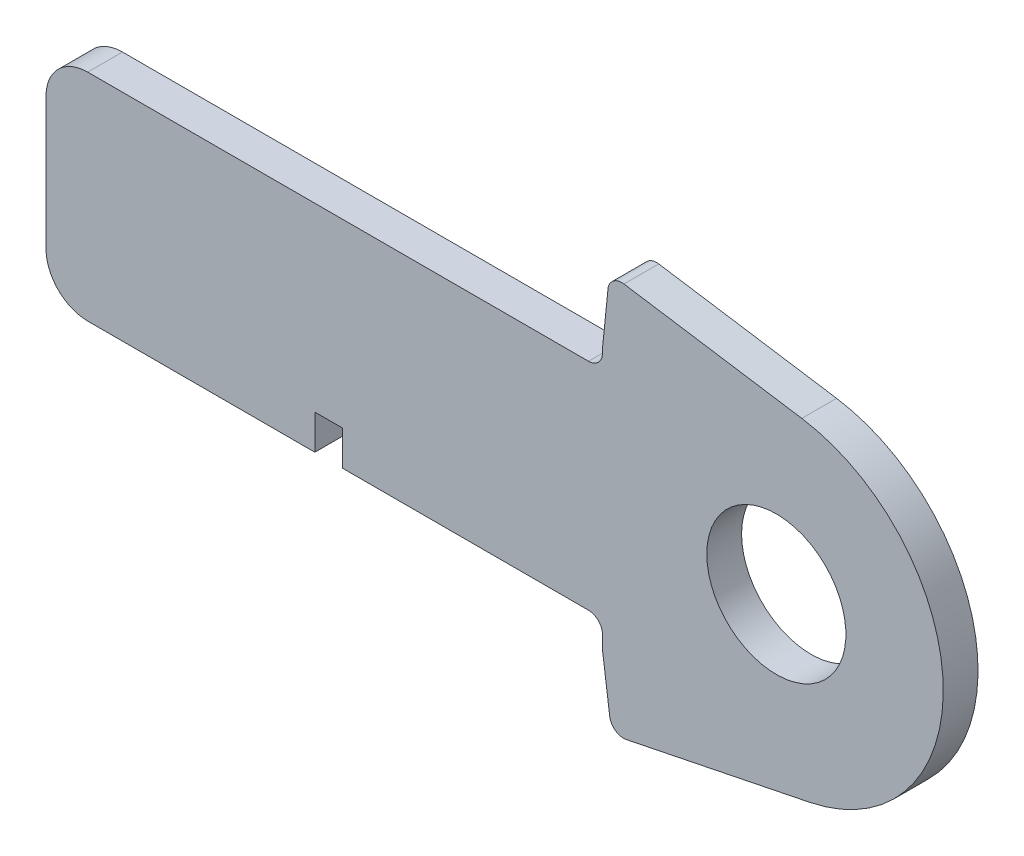
SolidWorks part; units mm, degrees
material "Plywood"
ref_plane "Front Plane" through (0, 0, 0) normal (0, 0, 1) x (1, 0, 0)
ref_plane "Top Plane" through (0, 0, 0) normal (0, 1, 0) x (1, 0, 0)
ref_plane "Right Plane" through (0, 0, 0) normal (1, 0, 0) x (0, 0, -1)
curve "Curve1"
  spline degree 3 poles (452.1031, 0.7048, 0) (452.0685, 0.7262, 0) (451.9301, 0.8117, 0) (451.6183, 1.003, 0) (451.099, 1.3216, 0) (450.372, 1.7653, 0) (449.438, 2.3329, 0) (448.2963, 3.0204, 0) (446.9478, 3.8257, 0) (445.3928, 4.7448, 0) (443.6314, 5.7736, 0) (441.6643, 6.9077, 0) (439.4916, 8.1409, 0) (437.1143, 9.468, 0) (434.5331, 10.8828, 0) (431.7485, 12.3789, 0) (428.7615, 13.9486, 0) (425.5733, 15.5853, 0) (422.1844, 17.2798, 0) (418.5964, 19.0251, 0) (414.8106, 20.8125, 0) (410.8282, 22.6325, 0) (406.6515, 24.4776, 0) (402.2816, 26.3365, 0) (397.7212, 28.201, 0) (392.972, 30.0605, 0) (388.0369, 31.9065, 0) (382.9178, 33.7272, 0) (377.6186, 35.5144, 0) (372.1418, 37.2567, 0) (366.4913, 38.9446, 0) (360.6704, 40.5671, 0) (354.684, 42.1159, 0) (348.5359, 43.5797, 0) (342.2312, 44.9487, 0) (335.775, 46.2147, 0) (329.1727, 47.3651, 0) (322.4425, 48.3989, 0) (315.6929, 49.2588, 0) (308.9571, 50.1023, 0) (302.2314, 50.8946, 0) (295.4235, 51.6533, 0) (288.5399, 52.3742, 0) (281.5875, 53.055, 0) (274.5733, 53.6928, 0) (267.5046, 54.2857, 0) (260.3883, 54.8303, 0) (253.2318, 55.3259, 0) (246.0422, 55.768, 0) (238.8272, 56.1563, 0) (231.5941, 56.4881, 0) (224.3504, 56.7611, 0) (217.1039, 56.9737, 0) (209.862, 57.1238, 0) (202.6326, 57.2105, 0) (195.4232, 57.2315, 0) (188.2416, 57.1863, 0) (181.0954, 57.0734, 0) (173.9924, 56.8912, 0) (166.9401, 56.6395, 0) (159.9462, 56.3182, 0) (153.0184, 55.9248, 0) (146.164, 55.4618, 0) (139.3909, 54.9271, 0) (132.7063, 54.3206, 0) (126.1174, 53.645, 0) (119.6314, 52.8983, 0) (113.2554, 52.0826, 0) (106.9962, 51.1996, 0) (100.8609, 50.2488, 0) (94.8561, 49.2329, 0) (88.9882, 48.153, 0) (83.2635, 47.0122, 0) (77.6882, 45.8109, 0) (72.2682, 44.5525, 0) (67.0092, 43.2395, 0) (61.9167, 41.874, 0) (56.9959, 40.4594, 0) (52.2519, 38.999, 0) (47.6902, 37.4943, 0) (43.3141, 35.951, 0) (39.1291, 34.3702, 0) (35.1384, 32.7568, 0) (31.3466, 31.113, 0) (27.7567, 29.4439, 0) (24.3726, 27.7512, 0) (21.1967, 26.0397, 0) (18.2324, 24.3122, 0) (15.4823, 22.5717, 0) (12.9477, 20.8227, 0) (10.632, 19.0664, 0) (8.5361, 17.307, 0) (6.6613, 15.5474, 0) (5.0102, 13.7886, 0) (3.5829, 12.0339, 0) (2.3811, 10.2847, 0) (1.4051, 8.5424, 0) (0.6571, 6.8085, 0) (0.1363, 5.084, 0) (-0.1488, 3.3712, 0) (-0.2197, 1.669, 0) (-0.0731, 0.5555, 0) (0, 0, 0) knots 0 0 0 0 0.000254 0.001015 0.002283 0.004057 0.006331 0.009105 0.012374 0.016134 0.02038 0.025106 0.030306 0.035972 0.0421 0.048678 0.055702 0.06316 0.071046 0.07935 0.088063 0.097176 0.106678 0.116562 0.126814 0.137428 0.148394 0.1597 0.171338 0.183298 0.19557 0.208144 0.221012 0.234162 0.247587 0.261277 0.275223 0.289414 0.303771 0.317689 0.331784 0.34604 0.360444 0.374983 0.38964 0.404403 0.419257 0.434187 0.449177 0.464215 0.479284 0.49437 0.509458 0.524532 0.539579 0.554583 0.56953 0.584403 0.599191 0.613877 0.628447 0.642889 0.657186 0.671326 0.685294 0.699078 0.712665 0.726043 0.739198 0.752118 0.764792 0.777208 0.789356 0.801224 0.812804 0.824083 0.835055 0.84571 0.856038 0.866034 0.875689 0.884998 0.893953 0.902553 0.910789 0.918661 0.926166 0.933303 0.940071 0.946475 0.952518 0.958205 0.963547 0.968557 0.97325 0.977651 0.981787 0.985694 0.989415 0.993001 0.996508 1 1 1 1
curve "Curve2"
  spline degree 3 poles (0, 0, 0) (0.1161, -0.5481, 0) (0.3488, -1.6467, 0) (0.9811, -3.2283, 0) (1.8173, -4.7487, 0) (2.8749, -6.2038, 0) (4.147, -7.5932, 0) (5.6306, -8.9184, 0) (7.3243, -10.1787, 0) (9.226, -11.3735, 0) (11.3328, -12.5041, 0) (13.6425, -13.5697, 0) (16.1528, -14.5701, 0) (18.8611, -15.5039, 0) (21.764, -16.3724, 0) (24.8588, -17.1737, 0) (28.1419, -17.9088, 0) (31.6103, -18.5759, 0) (35.26, -19.1755, 0) (39.0874, -19.7075, 0) (43.0885, -20.172, 0) (47.2594, -20.5682, 0) (51.596, -20.8969, 0) (56.0938, -21.1583, 0) (60.7487, -21.3533, 0) (65.556, -21.481, 0) (70.5112, -21.5436, 0) (75.6096, -21.5419, 0) (80.8464, -21.4754, 0) (86.2171, -21.3479, 0) (91.7164, -21.1586, 0) (97.3395, -20.9096, 0) (103.0813, -20.6036, 0) (108.9365, -20.2416, 0) (114.9002, -19.8251, 0) (120.967, -19.3576, 0) (127.1315, -18.8401, 0) (133.3883, -18.2757, 0) (139.7319, -17.6673, 0) (146.1567, -17.0167, 0) (152.6572, -16.327, 0) (159.2275, -15.6004, 0) (165.862, -14.8409, 0) (172.5546, -14.0497, 0) (179.2998, -13.2315, 0) (186.0911, -12.3877, 0) (192.923, -11.5217, 0) (199.7891, -10.6375, 0) (206.6832, -9.7349, 0) (213.5994, -8.8205, 0) (220.5311, -7.8935, 0) (227.4721, -6.9586, 0) (234.4161, -6.0188, 0) (241.3564, -5.0743, 0) (248.2868, -4.1291, 0) (255.2009, -3.1857, 0) (262.0918, -2.2442, 0) (268.9535, -1.3094, 0) (275.779, -0.3811, 0) (282.5619, 0.5389, 0) (289.2958, 1.4477, 0) (295.9744, 2.3443, 0) (302.5907, 3.228, 0) (309.138, 4.0992, 0) (315.5119, 4.9314, 0) (321.6955, 5.769, 0) (327.7099, 6.4556, 0) (333.6493, 7.0417, 0) (339.52, 7.5222, 0) (345.315, 7.9041, 0) (351.0275, 8.19, 0) (356.6509, 8.3839, 0) (362.1779, 8.4917, 0) (367.6017, 8.516, 0) (372.9148, 8.4647, 0) (378.1105, 8.3417, 0) (383.1813, 8.1528, 0) (388.1203, 7.9042, 0) (392.9205, 7.6027, 0) (397.5745, 7.2527, 0) (402.076, 6.8625, 0) (406.4179, 6.4377, 0) (410.5937, 5.9833, 0) (414.5972, 5.5086, 0) (418.4221, 5.0169, 0) (422.0625, 4.5163, 0) (425.5126, 4.0117, 0) (428.7669, 3.5097, 0) (431.8204, 3.015, 0) (434.6681, 2.5342, 0) (437.3055, 2.0718, 0) (439.7281, 1.6323, 0) (441.9324, 1.2212, 0) (443.9143, 0.8406, 0) (445.6709, 0.4968, 0) (447.199, 0.1913, 0) (448.4964, -0.0716, 0) (449.5609, -0.2909, 0) (450.3908, -0.463, 0) (450.9844, -0.5881, 0) (451.3411, -0.6626, 0) (451.4997, -0.6964, 0) (451.5393, -0.7048, 0) knots 0 0 0 0 0.003638 0.007293 0.011028 0.014901 0.018963 0.023258 0.027821 0.032679 0.037853 0.043362 0.049215 0.055422 0.061989 0.068918 0.076211 0.083868 0.091887 0.100266 0.109 0.118085 0.127515 0.137285 0.147388 0.157816 0.168563 0.179619 0.190977 0.202627 0.21456 0.226767 0.239236 0.251959 0.264924 0.27812 0.291536 0.30516 0.318981 0.332985 0.347163 0.361499 0.375981 0.390597 0.405333 0.420175 0.43511 0.450124 0.465203 0.480333 0.495501 0.51069 0.525887 0.541078 0.556247 0.571382 0.586466 0.601485 0.616424 0.631269 0.646007 0.660621 0.675098 0.689423 0.703582 0.716908 0.730009 0.742952 0.755726 0.76832 0.780724 0.792927 0.804916 0.816679 0.828204 0.839475 0.850481 0.861208 0.871639 0.881763 0.891564 0.901027 0.910139 0.918884 0.927249 0.935221 0.942785 0.949928 0.956638 0.962904 0.968712 0.974054 0.978918 0.983297 0.98718 0.990561 0.993433 0.995791 0.99763 0.998946 0.999737 1 1 1 1
sketch "Sketch1" plane through (0, 0, 0) normal (0, 0, 1) x (1, 0, 0)
  line L24 (435.3301, 0.6787) -> (439.1729, -1.6142)
  line L25 (434.7872, -0.6787) -> (439.1729, -1.6142)
  spline S4 degree 3 poles (0, 0) (0.1118, -0.5277) (0.3359, -1.5856) (0.9447, -3.1085) (1.7499, -4.5725) (2.7683, -5.9736) (3.9931, -7.3115) (5.4217, -8.5876) (7.0526, -9.8011) (8.8837, -10.9516) (10.9124, -12.0402) (13.1363, -13.0663) (15.5535, -14.0296) (18.1613, -14.9287) (20.9565, -15.765) (23.9365, -16.5366) (27.0978, -17.2444) (30.4375, -17.8867) (33.9519, -18.4641) (37.6373, -18.9763) (41.49, -19.4236) (45.5061, -19.8051) (49.6818, -20.1216) (54.0128, -20.3734) (58.4949, -20.5611) (63.1239, -20.6841) (67.8952, -20.7443) (72.8045, -20.7427) (77.847, -20.6787) (83.0184, -20.5559) (88.3137, -20.3736) (93.7282, -20.1339) (99.2569, -19.8392) (104.895, -19.4906) (110.6374, -19.0896) (116.4791, -18.6394) (122.4149, -18.1411) (128.4396, -17.5977) (134.5478, -17.0118) (140.7343, -16.3853) (146.9936, -15.7212) (153.3201, -15.0216) (159.7085, -14.2903) (166.1528, -13.5285) (172.6478, -12.7406) (179.1872, -11.9281) (185.7655, -11.0942) (192.377, -10.2428) (199.0153, -9.3738) (205.6749, -8.4933) (212.3494, -7.6007) (219.0329, -6.7005) (225.7193, -5.7955) (232.4021, -4.886) (239.0753, -3.9759) (245.7329, -3.0675) (252.3682, -2.161) (258.9753, -1.2608) (265.5476, -0.3669) (272.0789, 0.5189) (278.563, 1.394) (284.9937, 2.2573) (291.3645, 3.1082) (297.669, 3.9471) (303.8064, 4.7484) (309.7606, 5.555) (315.5518, 6.2161) (321.2709, 6.7805) (326.9238, 7.2431) (332.5038, 7.6108) (338.0044, 7.8861) (343.4191, 8.0729) (348.7411, 8.1767) (353.9637, 8.2001) (359.0797, 8.1506) (364.0826, 8.0323) (368.9653, 7.8503) (373.7211, 7.6109) (378.3431, 7.3206) (382.8245, 6.9836) (387.159, 6.6079) (391.3398, 6.1989) (395.3607, 5.7613) (399.2157, 5.3043) (402.8986, 4.8308) (406.404, 4.3487) (409.7261, 3.8629) (412.8597, 3.3795) (415.7999, 2.9031) (418.5419, 2.4402) (421.0815, 1.9949) (423.4142, 1.5717) (425.5368, 1.1759) (427.445, 0.8095) (429.1365, 0.4784) (430.6079, 0.1842) (431.8572, -0.0689) (432.8822, -0.2801) (433.6813, -0.4458) (434.2529, -0.5663) (434.5964, -0.638) (434.749, -0.6706) (434.7872, -0.6787) knots 0 0 0 0 0.003638 0.007293 0.011028 0.014901 0.018963 0.023258 0.027821 0.032679 0.037853 0.043362 0.049215 0.055422 0.061989 0.068918 0.076211 0.083868 0.091887 0.100266 0.109 0.118085 0.127515 0.137285 0.147388 0.157816 0.168563 0.179619 0.190977 0.202627 0.21456 0.226767 0.239236 0.251959 0.264924 0.27812 0.291536 0.30516 0.318981 0.332985 0.347163 0.361499 0.375981 0.390597 0.405333 0.420175 0.43511 0.450124 0.465203 0.480333 0.495501 0.51069 0.525887 0.541078 0.556247 0.571382 0.586466 0.601485 0.616424 0.631269 0.646007 0.660621 0.675098 0.689423 0.703582 0.716908 0.730009 0.742952 0.755726 0.76832 0.780724 0.792927 0.804916 0.816679 0.828204 0.839475 0.850481 0.861208 0.871639 0.881763 0.891564 0.901027 0.910139 0.918884 0.927249 0.935221 0.942785 0.949928 0.956638 0.962904 0.968712 0.974054 0.978918 0.983297 0.98718 0.990561 0.993433 0.995791 0.99763 0.998946 0.999737 1 1 1 1
  spline S5 degree 3 poles (435.3301, 0.6787) (435.2968, 0.6993) (435.1635, 0.7816) (434.8632, 0.9658) (434.3632, 1.2726) (433.6632, 1.6998) (432.7638, 2.2463) (431.6645, 2.9084) (430.3661, 3.6837) (428.8687, 4.5688) (427.1727, 5.5594) (425.2785, 6.6514) (423.1865, 7.8389) (420.8974, 9.1168) (418.4119, 10.4791) (415.7306, 11.9197) (412.8545, 13.4311) (409.7845, 15.0071) (406.5213, 16.6387) (403.0665, 18.3192) (399.4211, 20.0403) (395.5865, 21.7928) (391.5647, 23.5695) (387.357, 25.3594) (382.9657, 27.1547) (378.3927, 28.9452) (373.6407, 30.7228) (368.7116, 32.4759) (363.609, 34.1968) (358.3353, 35.8745) (352.8945, 37.4998) (347.2896, 39.0621) (341.5252, 40.5534) (335.6052, 41.9629) (329.5344, 43.2811) (323.3177, 44.5002) (316.9603, 45.6079) (310.4799, 46.6033) (303.9807, 47.4313) (297.4948, 48.2435) (291.0186, 49.0064) (284.4633, 49.737) (277.8351, 50.4311) (271.1406, 51.0867) (264.3866, 51.7008) (257.5802, 52.2717) (250.7279, 52.7961) (243.8369, 53.2733) (236.914, 53.699) (229.9667, 54.0729) (223.0019, 54.3924) (216.027, 54.6553) (209.0493, 54.86) (202.0761, 55.0045) (195.1149, 55.088) (188.173, 55.1082) (181.2578, 55.0647) (174.3767, 54.956) (167.5373, 54.7806) (160.7467, 54.5381) (154.0122, 54.2288) (147.3414, 53.85) (140.7414, 53.4041) (134.2195, 52.8893) (127.7829, 52.3053) (121.4385, 51.6548) (115.1931, 50.9357) (109.0536, 50.1503) (103.0266, 49.3001) (97.119, 48.3846) (91.3369, 47.4064) (85.6868, 46.3665) (80.1745, 45.2681) (74.806, 44.1113) (69.5871, 42.8996) (64.5231, 41.6353) (59.6196, 40.3205) (54.8814, 38.9584) (50.3134, 37.5521) (45.9209, 36.1032) (41.7071, 34.6172) (37.6774, 33.0951) (33.8348, 31.5415) (30.1837, 29.9587) (26.7269, 28.3515) (23.4684, 26.7216) (20.4104, 25.0737) (17.5559, 23.4102) (14.9079, 21.7343) (12.4673, 20.0502) (10.2376, 18.359) (8.2194, 16.6649) (6.4142, 14.9706) (4.8244, 13.2771) (3.45, 11.5875) (2.2928, 9.9031) (1.353, 8.2255) (0.6327, 6.5559) (0.1312, 4.8953) (-0.1433, 3.2462) (-0.2116, 1.607) (-0.0704, 0.5349) (0, 0) knots 0 0 0 0 0.000254 0.001015 0.002283 0.004057 0.006331 0.009105 0.012374 0.016134 0.02038 0.025106 0.030306 0.035972 0.0421 0.048678 0.055702 0.06316 0.071046 0.07935 0.088063 0.097176 0.106678 0.116562 0.126814 0.137428 0.148394 0.1597 0.171338 0.183298 0.19557 0.208144 0.221012 0.234162 0.247587 0.261277 0.275223 0.289414 0.303771 0.317689 0.331784 0.34604 0.360444 0.374983 0.38964 0.404403 0.419257 0.434187 0.449177 0.464215 0.479284 0.49437 0.509458 0.524532 0.539579 0.554583 0.56953 0.584403 0.599191 0.613877 0.628447 0.642889 0.657186 0.671326 0.685294 0.699078 0.712665 0.726043 0.739198 0.752118 0.764792 0.777208 0.789356 0.801224 0.812804 0.824083 0.835055 0.84571 0.856038 0.866034 0.875689 0.884998 0.893953 0.902553 0.910789 0.918661 0.926166 0.933303 0.940071 0.946475 0.952518 0.958205 0.963547 0.968557 0.97325 0.977651 0.981787 0.985694 0.989415 0.993001 0.996508 1 1 1 1
extrude "Boss-Extrude1" add sketch "Sketch1" along normal blind 3.175
sketch "Sketch2" plane through (0, 0, 0) normal (0, 0, -1) x (-1, 0, 0)
  line L0 (-252.7944, 13.2215) -> (-250.2544, 13.2215)
  line L1 (-250.2544, -2.1152) -> (-250.2544, -3.9863)
  line L2 (-252.7944, 13.2215) -> (-252.7944, -2.1152)
  line L4 (-250.2544, -3.9863) -> (-252.7944, -3.0508)
  line L5 (-252.7944, -3.0508) -> (-252.7944, -2.1152)
  line L7 (-159.1319, 54.4222) -> (-159.1319, 39.0391)
  line L8 (-159.1319, 39.0391) -> (-152.7819, 39.0391)
  line L9 (-152.7819, 54.4222) -> (-152.7819, 57.6454)
  line L10 (-74.9944, -5.9288) -> (-74.9944, -20.1418)
  line L12 (-152.7819, 57.6454) -> (-159.1319, 55.5409)
  line L13 (-159.1319, 55.5409) -> (-159.1319, 54.4222)
  line L14 (-71.8194, -5.9288) -> (-71.8194, -20.1418)
  line L16 (-74.9944, -5.9288) -> (-71.8194, -5.9288)
  line L17 (-71.8194, -20.1418) -> (-71.8194, -22.1459)
  line L19 (-152.7819, 54.4222) -> (-152.7819, 39.0391)
  line L20 (-71.8194, -22.1459) -> (-74.9944, -20.9764)
  line L21 (-74.9944, -20.9764) -> (-74.9944, -20.1418)
  line L22 (-250.2544, 13.2215) -> (-250.2544, -2.1152)
extrude "Cut-Extrude1" cut sketch "Sketch2" against normal blind 7.62
sketch "Sketch3" plane through (0, 0, 0) normal (0, 0, -1) x (-1, 0, 0)
  circle A1 centre (-292.3838, 26.2554) radius 6.35
extrude "Cut-Extrude2" cut sketch "Sketch3" against normal blind 7.62
sketch "Sketch4" plane through (0, 0, 3.175) normal (0, 0, 1) x (1, 0, 0)
  line L0 (274.6066, 50.6647) -> (273.3497, 38.0281)
  line L1 (274.6066, 50.6647) -> (273.3497, 38.0281)
  line L2 (276.5088, 37.7139) -> (277.7874, 50.3428)
  line L3 (276.5088, 37.7139) -> (277.7874, 50.3428)
  line L4 (278.2022, 1.3477) -> (276.5088, 13.9346)
  line L5 (278.2022, 1.3477) -> (276.5088, 13.9346)
  line L6 (273.3622, 13.5108) -> (275.0576, 0.9245)
  line L7 (273.3622, 13.5108) -> (275.0576, 0.9245)
  line L14 (277.1481, 44.0283) -> (294.7093, 41.317)
  line L22 (225.7088, 36.0979) -> (276.5088, 36.0979)
  line L24 (225.7088, 36.0979) -> (225.7088, 16.4129)
  line L26 (225.7088, 16.4129) -> (276.5088, 16.4129)
  line L32 (277.3555, 7.6412) -> (295.4257, 11.3221)
  line L34 (276.5088, 13.9346) -> (276.5088, 37.7139)
  line L35 (273.3497, 38.0281) -> (276.5088, 37.7139)
  line L36 (276.5088, 13.9346) -> (273.3622, 13.5108)
  line L37 (275.0576, 0.9245) -> (278.2022, 1.3477)
  line L49 (277.7874, 50.3428) -> (274.6066, 50.6647)
  line L50 (250.2544, 13.2215) -> (250.2544, 19.5879)
  line L51 (225.7088, 31.0179) -> (263.8088, 31.0179)
  line L52 (225.7088, 31.0179) -> (225.7088, 21.4929)
  line L53 (225.7088, 21.4929) -> (263.8088, 21.4929)
  line L54 (263.8088, 31.0179) -> (263.8088, 21.4929)
  line L55 (250.2544, 19.5879) -> (252.7944, 19.5879)
  line L56 (252.7944, 19.5879) -> (252.7944, 13.2215)
  circle A0 centre (292.3838, 26.2554) radius 6.35 construction
  circle A1 centre (292.3838, 26.2554) radius 6.35
  circle A2 centre (292.3838, 26.2554) radius 15.24
  point P12 (225.7088, 26.2554)
  point P13 (225.7088, 26.2554)
  point P40 (263.8088, 26.2554)
  dimension "D6" = 30.48
  dimension "D1" = 9.525
  dimension "D2" = 38.1
  dimension "D3" = 12.7
  dimension "D4" = 5.08
  dimension "D5" = 3.175
extrude "Cut-Extrude3" cut sketch "Sketch4" against normal through all
fillet "Fillet1" radius 3.81 2 edges at (225.7088, 16.4129, 1.5875) (225.7088, 36.0979, 1.5875)
fillet "Fillet2" radius 1.27 4 edges at (277.3555, 7.6412, 1.5875) (277.1481, 44.0283, 1.5875) (276.5088, 16.4129, 1.5875) (276.5088, 36.0979, 1.5875)
move or copy body "Body-Move/Copy1" [suppressed] bodies to move or copy 120 parameters "D1"=0, "D2"=0, "D3"=0
move or copy body "Body-Move/Copy2" [suppressed] bodies to move or copy 121 parameters "D1"=0, "D2"=0, "D3"=0
